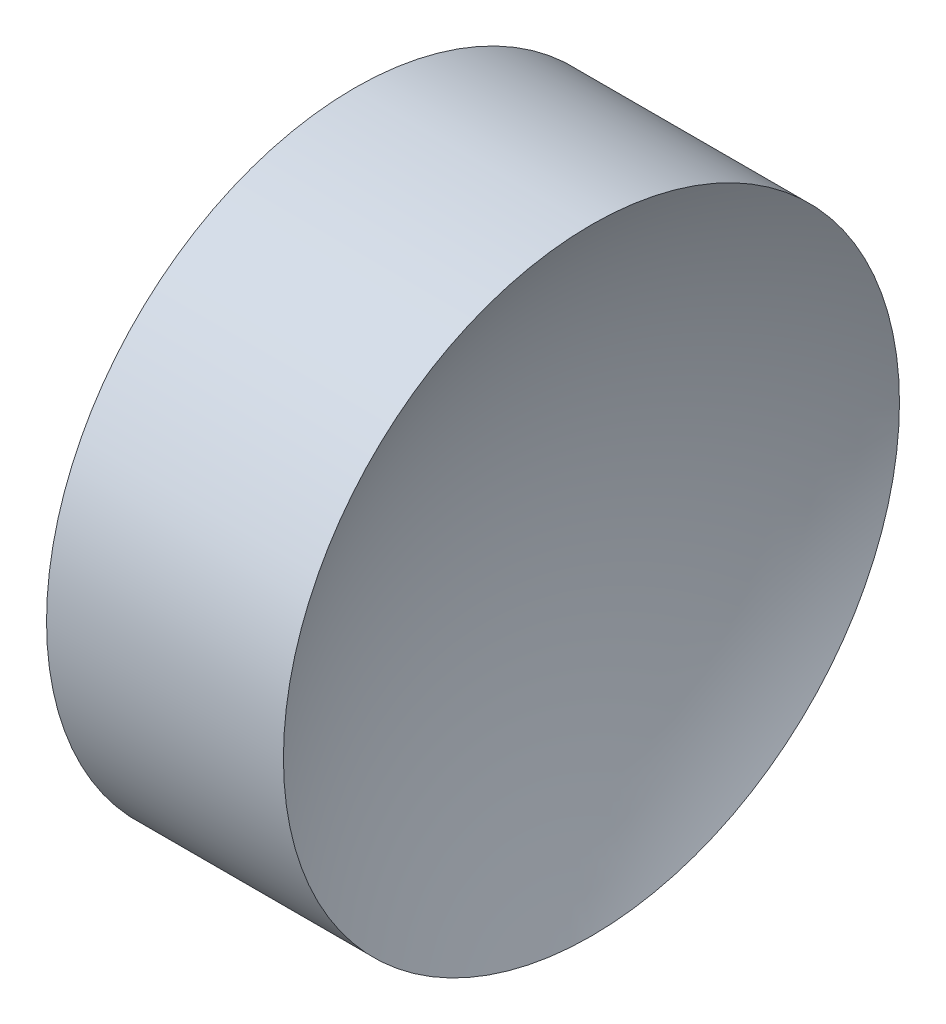
SolidWorks part; units mm, degrees
ref_plane "前视基准面" through (0, 0, 0) normal (0, 0, 1) x (1, 0, 0)
ref_plane "上视基准面" through (0, 0, 0) normal (0, 1, 0) x (1, 0, 0)
ref_plane "右视基准面" through (0, 0, 0) normal (1, 0, 0) x (0, 0, -1)
sketch "草图1" plane through (0, 0, 0) normal (0, 0, 1) x (1, 0, 0)
  line L0 (53.0623, 32.6113) -> (69.5807, 32.6113) construction
  line L1 (60.8516, 32.6113) -> (59.3516, 32.6113)
  line L3 (60.1016, 38.8613) -> (62.5049, 38.8613)
  line L4 (60.1016, 38.8613) -> (57.6983, 38.8613)
  arc A0 (62.5049, 38.8613) -> (60.8516, 32.6113) centre (73.4916, 32.6113) ccw
  arc A1 (59.3516, 32.6113) -> (57.6983, 38.8613) centre (46.7116, 32.6113) ccw
revolve "旋转1" add sketch "草图1" angle 360 about L0
